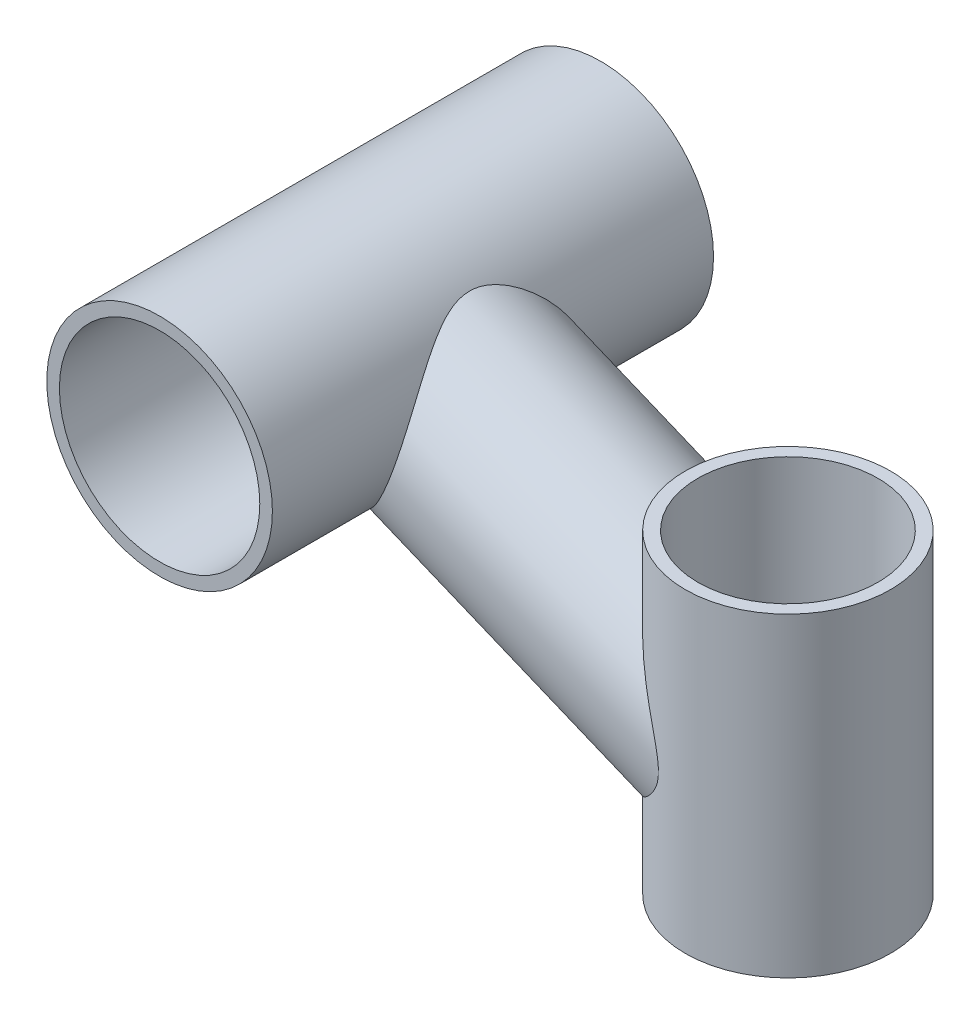
SolidWorks part; units mm, degrees
material "1060 Alloy"
ref_plane "Plan de face" through (0, 0, 0) normal (0, 0, 1) x (1, 0, 0)
ref_plane "Plan de dessus" through (0, 0, 0) normal (0, 1, 0) x (1, 0, 0)
ref_plane "Plan de droite" through (0, 0, 0) normal (1, 0, 0) x (0, 0, -1)
sketch "Esquisse1" plane through (0, 0, 0) normal (0, 0, 1) x (1, 0, 0)
  circle A0 centre (0, 0) radius 15.9
  circle A1 centre (0, 0) radius 17.9
  dimension "D1" = 31.8
  dimension "D2" = 2
sketch "Esquisse2" plane through (0, 0, 0) normal (1, 0, 0) x (0, 0, -1)
  line L0 (-35, 0) -> (35, 0)
  point P4 (0, 0)
  point P5 (0, 0)
sweep "Balayage1" add profiles "Esquisse1" path "Esquisse2"
sketch "Esquisse3" plane through (0, 0, 0) normal (0, 0, 1) x (1, 0, 0)
  line L0 (0, 0) -> (64.7023, -26.7134)
  dimension "D1" = 70
ref_plane "Plan1" through (0, -26.7134, 0) normal (0, 1, 0) x (1, 0, 0)
sketch "Esquisse5" plane through (0, -26.7134, 0) normal (0, 1, 0) x (1, 0, 0)
  line L0 (0, 0) -> (64.7023, 0) construction
  circle A0 centre (64.7023, 0) radius 14.3
  circle A1 centre (64.7023, 0) radius 16.3
  dimension "D1" = 28.6
  dimension "D2" = 2
ref_plane "Plan2" through (0, 0, 0) normal (0, 0, 1) x (1, 0, 0)
sketch "Esquisse6" plane through (0, 0, 0) normal (0, 0, 1) x (1, 0, 0)
  line L0 (64.7023, -29.7134) -> (64.7023, -23.7134)
  point P3 (64.7023, -26.7134)
  dimension "D1" = 6
sketch "Esquisse7" plane through (0, 0, 0) normal (0, 0, 1) x (1, 0, 0)
  line L0 (0, 0) -> (64.7023, -26.7134) construction
  point P0 (32.3512, -13.3567)
ref_plane "Plan3" through (32.3512, -13.3567, 0) normal (0.9243, -0.3816, 0) x (0, 0, -1)
sketch "Esquisse8" plane through (32.3512, -13.3567, 0) normal (0.9243, -0.3816, 0) x (0, 0, -1)
  circle A0 centre (0, 0) radius 15.5
  circle A1 centre (0, 0) radius 12.5
  dimension "D1" = 3
  dimension "D2" = 25
extrude "Boss.-Extru.1" add sketch "Esquisse5" along normal blind 30 and the other way blind 20 separate body contours A0 | A1
extrude "Boss.-Extru.2" add sketch "Esquisse8" along normal up to next and the other way up to next contours A0 | A1
